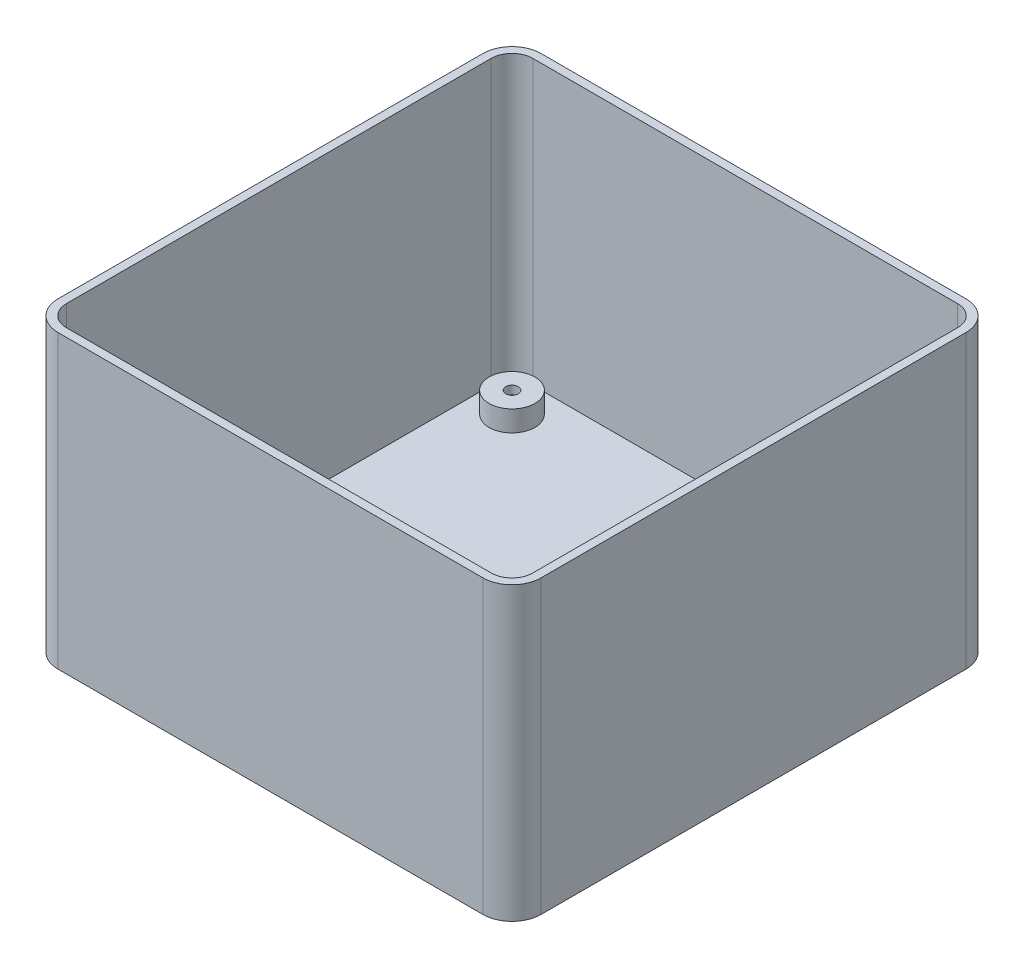
SolidWorks part; units mm, degrees
ref_plane "Front Plane" through (0, 0, 0) normal (0, 0, 1) x (1, 0, 0)
ref_plane "Top Plane" through (0, 0, 0) normal (0, 1, 0) x (1, 0, 0)
ref_plane "Right Plane" through (0, 0, 0) normal (1, 0, 0) x (0, 0, -1)
sketch "Sketch1" plane through (0, 0, 0) normal (0, 1, 0) x (1, 0, 0)
  line L5 (-51, 58) -> (51, 58)
  line L6 (-51, -56) -> (51, -56)
  line L10 (-56, -51) -> (-56, 51)
  line L11 (-51, 56) -> (51, 56)
  line L12 (56, -51) -> (56, 51)
  line L13 (-56, -56) -> (56, 56) construction
  line L14 (-56, 56) -> (56, -56) construction
  line L15 (58, -51) -> (58, 51)
  line L16 (-51, -58) -> (51, -58)
  line L17 (-58, -51) -> (-58, 51)
  arc A0 (-51, -56) -> (-56, -51) centre (-51, -51) cw
  arc A1 (51, -56) -> (56, -51) centre (51, -51) ccw
  arc A2 (51, 56) -> (56, 51) centre (51, 51) cw
  arc A3 (-56, 51) -> (-51, 56) centre (-51, 51) cw
  arc A4 (51, 58) -> (58, 51) centre (51, 51) cw
  arc A5 (51, -58) -> (58, -51) centre (51, -51) ccw
  arc A6 (-51, -58) -> (-58, -51) centre (-51, -51) cw
  arc A7 (-58, 51) -> (-51, 58) centre (-51, 51) cw
  point P0 (0, 0)
  dimension "D1" = 112
  dimension "D4" = 2
  dimension "D3" = 5
  dimension "D2" = 112
extrude "Boss-Extrude1" add sketch "Sketch1" along normal blind 70
sketch "Sketch2" plane through (0, 70, 0) normal (0, 1, 0) x (1, 0, 0)
  line L4 (-58, 51) -> (-58, -51)
  line L5 (-51, -58) -> (51, -58)
  line L6 (58, -51) -> (58, 51)
  line L7 (51, 58) -> (-51, 58)
  line L8 (-58, 51) -> (-58, -51)
  line L9 (-51, -58) -> (51, -58)
  line L10 (58, -51) -> (58, 51)
  line L11 (51, 58) -> (-51, 58)
  arc A4 (-51, 58) -> (-58, 51) centre (-51, 51) ccw
  arc A5 (-58, -51) -> (-51, -58) centre (-51, -51) ccw
  arc A6 (51, -58) -> (58, -51) centre (51, -51) ccw
  arc A7 (58, 51) -> (51, 58) centre (51, 51) ccw
  arc A8 (-51, 58) -> (-58, 51) centre (-51, 51) ccw
  arc A9 (-58, -51) -> (-51, -58) centre (-51, -51) ccw
  arc A10 (51, -58) -> (58, -51) centre (51, -51) ccw
  arc A11 (58, 51) -> (51, 58) centre (51, 51) ccw
  dimension "D1" = 0
sketch "Sketch3" plane through (0, 0, 0) normal (0, 1, 0) x (1, 0, 0)
  line L0 (-58, 51) -> (-58, -51) construction
  line L1 (-51, -58) -> (51, -58) construction
  line L2 (58, -51) -> (58, 51) construction
  line L3 (51, 58) -> (-51, 58) construction
  line L4 (51, 58) -> (-51, 58)
  line L5 (-58, 51) -> (-58, -51)
  line L6 (-51, -58) -> (51, -58)
  line L7 (58, -51) -> (58, 51)
  arc A0 (-58, -51) -> (-51, -58) centre (-51, -51) ccw construction
  arc A1 (51, -58) -> (58, -51) centre (51, -51) ccw construction
  arc A2 (58, 51) -> (51, 58) centre (51, 51) ccw construction
  arc A3 (-51, 58) -> (-58, 51) centre (-51, 51) ccw construction
  arc A4 (-51, 58) -> (-58, 51) centre (-51, 51) ccw
  arc A5 (-58, -51) -> (-51, -58) centre (-51, -51) ccw
  arc A6 (51, -58) -> (58, -51) centre (51, -51) ccw
  arc A7 (58, 51) -> (51, 58) centre (51, 51) ccw
extrude "Boss-Extrude2" add sketch "Sketch3" along normal blind 2
sketch "Sketch5" plane through (0, 2, 0) normal (0, 1, 0) x (1, 0, 0)
  line L0 (-51, 51) -> (51, -51) construction
  line L1 (51, 51) -> (-51, -51) construction
  line L2 (-56, 51) -> (-56, -51) construction
  circle A0 centre (-47.5, 47.5) radius 1.5
  circle A1 centre (-47.5, 47.5) radius 5.5
  dimension "D2" = 3
  dimension "D3" = 11
  dimension "D1" = 8.5
extrude "Boss-Extrude3" add sketch "Sketch5" along normal blind 5
sketch "Sketch8" plane through (0, 0, 0) normal (0, 1, 0) x (1, 0, 0)
  circle A0 centre (-47.5, 47.5) radius 4.5
  dimension "D1" = 9
extrude "Cut-Extrude3" cut sketch "Sketch8" along normal offset from surface (5 mm away) 2 up to face at (-47.5, 7, -42)
